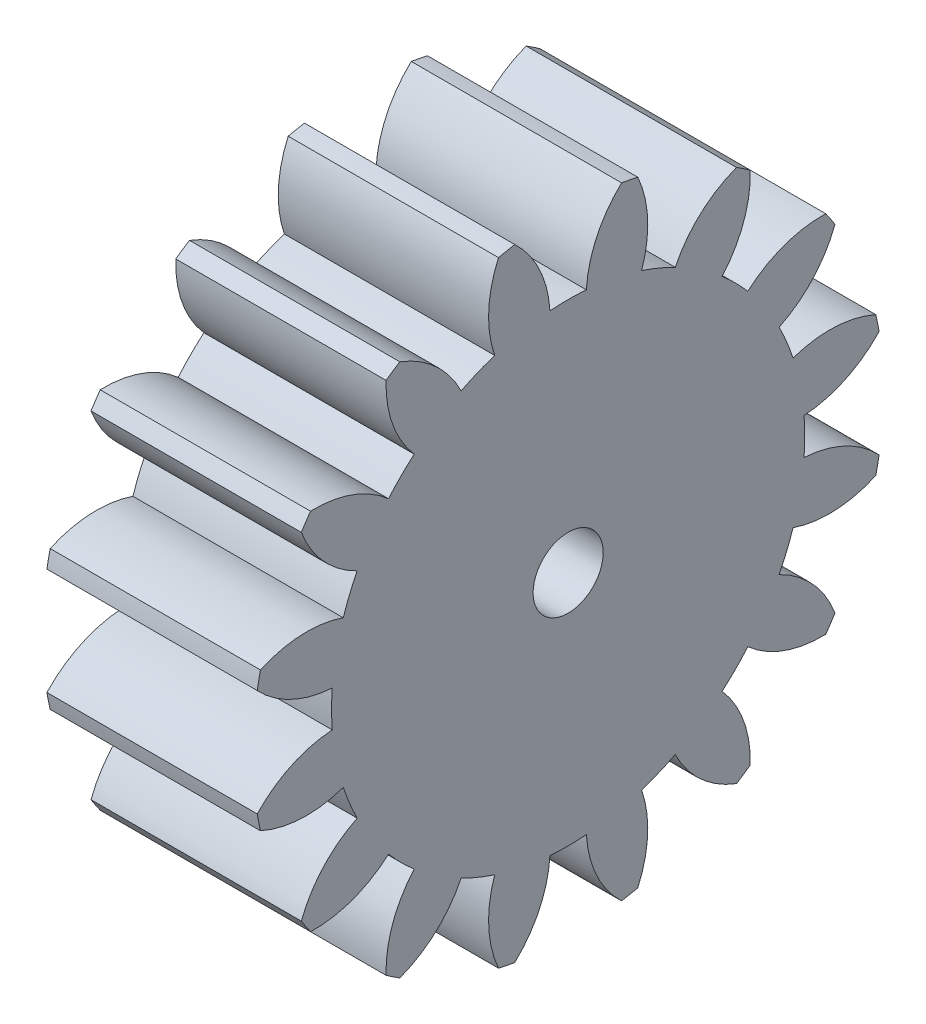
SolidWorks part; units mm, degrees
ref_plane "Plane1" through (0, 0, 0) normal (0, 0, 1) x (1, 0, 0)
ref_plane "Plane2" through (0, 0, 0) normal (0, 1, 0) x (1, 0, 0)
ref_plane "Plane3" through (0, 0, 0) normal (1, 0, 0) x (0, 0, -1)
sketch "HoldingSke" plane through (0, 0, 0) normal (0, 1, 0) x (1, 0, 0)
  line L0 (0, 0) -> (0.3845, -0.1103)
  line L1 (-15, 0) -> (100, 0) construction
  line L2 (0, 0) -> (-2.1039, 2.3779)
  line L3 (0, 0) -> (-11.863, 4.5341)
  line L4 (0, 0) -> (8.3015, 2.3804)
  line L5 (0, 0) -> (-46.8476, -17.4728)
  line L6 (0, 0) -> (-12.4344, -8.3896)
  line L7 (-2.1039, 2.3779) -> (8.6586, 51.2059)
  line L8 (-76.2, 54.61) -> (-75.3, 54.61)
  line L9 (-71.009, 38.7566) -> (-53.1078, 45.2721)
  line L10 (-76.2, 71.12) -> (104.1128, 71.12)
  line L11 (0, 0) -> (-15, 0)
  line L12 (-76.2, 101.6) -> (-76.113, 101.6)
  line L13 (24.9733, 27.94) -> (52.9518, 28.4284)
  line L14 (24.9733, 27.94) -> (24.9743, 27.94)
  line L15 (24.9733, 27.94) -> (100.4006, 29.5858)
  line L16 (-63.627, -2.5) -> (-12.827, -2.5)
  circle A0 centre (0, 0) radius 2.5
  circle A1 centre (0, 0) radius 16.874
  circle A2 centre (0, 0) radius 37.5
  circle A3 centre (0, 0) radius 2.5
  dimension "MHD" = 33.748
  dimension "Hub_dia" = 75
  dimension "Bore" = 5
  dimension "MBD" = 5
  dimension "Num_teeth" = 16
  dimension "Pitch" = 0.4
  dimension "Overall_len" = 50
  dimension "Show_teeth" = 16
  dimension "Thickness" = 15
  dimension "OAL" = 50.0001
  dimension "T_dim" = 0.9
  dimension "Ap" = 20
  dimension "H" = 19.05
  dimension "Pitch_radius" = 180.3128
  dimension "Width" = 15
  dimension "Backlash" = 0.087
  dimension "Addendum_fac" = 1
  dimension "Dedendum_fac" = 1.25
  dimension "Clearance_fac" = 0.25
  dimension "Dedendum_add" = 0.001
  dimension "Module" = 2.5
sketch "BasProSke" plane through (0, 0, 0) normal (0, 1, 0) x (1, 0, 0)
  line L0 (-10, 0) -> (60, 0) construction
  line L1 (0, 0) -> (0, 22.5)
  line L2 (0, 0) -> (15, 0)
  line L3 (15, 0) -> (15, 22.5)
  line L4 (15, 22.5) -> (0, 22.5)
  dimension "Thickness" = 15
  dimension "Diameter" = 45
revolve "Base-Revolve" add sketch "BasProSke" angle 360 about L0
sketch "TooCutSke" plane through (0, 0, 0) normal (1, 0, 0) x (0, 0, -1)
  line L1 (0, 0) -> (0, 107) construction
  line L2 (0, 0) -> (-2.1125, 19.8881) construction
  line L3 (0, 0) -> (-7.7717, 39.0708) construction
  line L4 (-2.1125, 19.8881) -> (-3.8858, 19.5354) construction
  arc A0 (1.2977, 16.824) -> (-1.2977, 16.824) centre (0, 0) ccw
  arc A1 (3.8326, 22.197) -> (-3.8326, 22.197) centre (0, 0) ccw
  circle A2 centre (0, 0) radius 20 construction
  circle A3 centre (0, 0) radius 18.7939 construction
  arc A4 (-1.2977, 16.824) -> (-3.8326, 22.197) centre (-9.2832, 16.3411) ccw
  arc A5 (3.8326, 22.197) -> (1.2977, 16.824) centre (9.2832, 16.3411) ccw
  dimension "Root_dia" = 33.748
  dimension "Overcut_dia" = 45.0508
  dimension "Pitch_dia" = 40
  dimension "Base_dia" = 37.5877
  dimension "Flank_rad" = 8
  dimension "Half_ang" = 11.25
  dimension "Half_CT" = 1.8081
extrude "ToothCut" cut sketch "TooCutSke" along normal through all
fillet "Breaks" [suppressed] radius 0.05
fillet "RootFillets" [suppressed] radius 0.626
pattern_circular "TeethCuts" count 16 every 22.5 about axis through (-10, 0, 0) along (1, 0, 0) of "ToothCut", "RootFillets", "Breaks"
sketch "HubNeaOneSke" plane through (0, 0, 0) normal (-1, 0, 0) x (0, 0, 1)
  circle A0 centre (0, 0) radius 16.874
  dimension "Diameter" = 33.748
extrude "HubNearOne" [suppressed] add sketch "HubNeaOneSke" along normal blind 35.0001
sketch "HubNeaBotSke" plane through (0, 0, 0) normal (-1, 0, 0) x (0, 0, 1)
  circle A0 centre (0, 0) radius 16.874
  dimension "Diameter" = 33.748
extrude "HubNearBoth" [suppressed] add sketch "HubNeaBotSke" along normal blind 17.5
ref_plane "FarPln" through (15, 0, 0) normal (1, 0, 0) x (0, 0, -1)
sketch "HubFarSke" plane through (15, 0, 0) normal (1, 0, 0) x (0, 0, -1)
  circle A0 centre (0, 0) radius 16.874
  dimension "Diameter" = 33.748
extrude "HubFar" [suppressed] add sketch "HubFarSke" along normal blind 17.5
sketch "BorSke" plane through (0, 0, 0) normal (1, 0, 0) x (0, 0, -1)
  circle A0 centre (0, 0) radius 2.5
  dimension "Diameter" = 5
extrude "Bore" cut sketch "BorSke" along normal mid plane 100.0001
sketch "KeySke" plane through (0, 0, 0) normal (1, 0, 0) x (0, 0, -1)
  line L0 (-1, 0) -> (-1, 3.4)
  line L1 (-1, 3.4) -> (1, 3.4)
  line L2 (1, 3.4) -> (1, 0)
  line L3 (0, 0) -> (0, 34) construction
  line L4 (-1, 0) -> (1, 0)
  dimension "Offset" = 3.4
  dimension "Width" = 2
extrude "Keyway" [suppressed] cut sketch "KeySke" along normal mid plane 100.0001
pattern_circular "Keyway2" [suppressed] count 2 every 90 about axis through (-10, 0, 0) along (1, 0, 0)
equation "' \"Module@HoldingSke\" = 6.35"
equation "' \"Num_teeth@HoldingSke\" = 12"
equation "' \"Ap@HoldingSke\" =  20"
equation "' \"Ap@HoldingSke\" = 20"
equation "' \"Width@HoldingSke\" = 0.5 * 25.4"
equation "' \"Hub_dia@HoldingSke\"= 1 * 25.4"
equation "' \"Hub_dia@HoldingSke\" = 1 * 25.4"
equation "' \"Overall_len@HoldingSke\" = 1.0 * 25.4"
equation "' \"Bore@HoldingSke\" = 0.75 * 25.4"
equation "' \"T_dim@HoldingSke\" = 0.1 * 25.4"
equation "' \"Width@KeySke\" = 0.25 * 25.4"
equation "' \"Show_teeth@HoldingSke\" = 13"
equation "' \"Backlash@HoldingSke\" = 0.009 * 25.4"
equation "' \"Addendum_fac@HoldingSke\" = 1.0"
equation "' \"Dedendum_fac@HoldingSke\" = 1.25"
equation "' \"Dedendum_add@HoldingSke\" = 0.00005 * 25.4"
equation "' \"Clearance_fac@HoldingSke\" = 0.25"
equation "\"Pitch@HoldingSke\" = 1 / \"Module@HoldingSke\""
equation "\"Overcut_dia@TooCutSke\" = (\"Num_teeth@HoldingSke\" + 2 * \"Addendum_fac@HoldingSke\") / \"Pitch@HoldingSke\" + 0.002 * 25.4"
equation "\"Pitch_dia@TooCutSke\" = \"Num_teeth@HoldingSke\" / \"Pitch@HoldingSke\""
equation "\"Base_dia@TooCutSke\" = \"Num_teeth@HoldingSke\" / \"Pitch@HoldingSke\" * cos((\"Ap@HoldingSke\"  * 3.14159265 / 180))"
equation "\"Root_dia@TooCutSke\" = (\"Num_teeth@HoldingSke\" + 2) / \"Pitch@HoldingSke\" - 2 * (\"Addendum_fac@HoldingSke\" + \"Dedendum_fac@HoldingSke\") / \"Pitch@HoldingSke\" - \"Dedendum_add@HoldingSke\" * 2"
equation "\"Half_ang@TooCutSke\" = 180 / \"Num_teeth@HoldingSke\""
equation "\"Half_CT@TooCutSke\" = \"Num_teeth@HoldingSke\" / \"Pitch@HoldingSke\" * sin((3.14159265 / 2 / \"Num_teeth@HoldingSke\")) / 2 - 7 * \"Backlash@HoldingSke\" / 4"
equation "\"Flank_rad@TooCutSke\" = \"Num_teeth@HoldingSke\" / \"Pitch@HoldingSke\" / 5"
equation "\"Radius@RootFillets\" = \"Clearance_fac@HoldingSke\" / \"Pitch@HoldingSke\" + \"Dedendum_add@HoldingSke\""
equation "\"Break_rad@Breaks\" = 0.02 / \"Pitch@HoldingSke\""
equation "\"Thickness@HoldingSke\" = \"Width@HoldingSke\""
equation "\"OAL@HoldingSke\" = \"Thickness@HoldingSke\""
equation "\"MHD@HoldingSke\" = (\"Num_teeth@HoldingSke\" + 2) / \"Pitch@HoldingSke\" - 2 * (\"Addendum_fac@HoldingSke\" + \"Dedendum_fac@HoldingSke\")  / \"Pitch@HoldingSke\" - \"Dedendum_add@HoldingSke\" * 2"
equation "\"MBD@HoldingSke\" = (\"Num_teeth@HoldingSke\" + 2) / \"Pitch@HoldingSke\" - 2 * (\"Addendum_fac@HoldingSke\" + \"Dedendum_fac@HoldingSke\")  / \"Pitch@HoldingSke\" - \"Dedendum_add@HoldingSke\" * 2 - 0.002 * 25.4"
equation "\"MHD@HoldingSke\" = ((sgn( \"MHD@HoldingSke\" - \"Hub_dia@HoldingSke\" )-1)*( \"MHD@HoldingSke\" - \"Hub_dia@HoldingSke\" ))/-2+ \"Hub_dia@HoldingSke\""
equation "\"MBD@HoldingSke\" = ((sgn( \"MBD@HoldingSke\" - \"Bore@HoldingSke\" )-1)*( \"MBD@HoldingSke\" - \"Bore@HoldingSke\" ))/-2+ \"Bore@HoldingSke\""
equation "\"OAL@HoldingSke\" = ((sgn( \"OAL@HoldingSke\" - \"Overall_len@HoldingSke\" )+1)*( \"OAL@HoldingSke\" - \"Overall_len@HoldingSke\" ))/2 + \"Overall_len@HoldingSke\" + 0.000002 * 25.4"
equation "\"Num_teeth@TeethCuts\" = int( \"Show_teeth@HoldingSke\" ) + 1"
equation "\"Num_teeth@TeethCuts\" = ((sgn( \"Num_teeth@TeethCuts\" - \"Num_teeth@HoldingSke\" )-1)*( \"Num_teeth@TeethCuts\" - \"Num_teeth@HoldingSke\" ))/-2+ \"Num_teeth@HoldingSke\""
equation "\"Num_teeth@TeethCuts\" = ((sgn( \"Num_teeth@TeethCuts\" - 2.0)+1)*( \"Num_teeth@TeethCuts\" - 2.0))/2 +2.0"
equation "\"Angle@TeethCuts\" = 360.0 / \"Num_teeth@HoldingSke\""
equation "\"Diameter@BasProSke\" = (\"Num_teeth@HoldingSke\" + 2 * \"Addendum_fac@HoldingSke\") / \"Pitch@HoldingSke\""
equation "\"Thickness@BasProSke\"  = \"Thickness@HoldingSke\""
equation "' \"Fillet_rad@BasProSke\" =  \"Thickness@HoldingSke\" * 0.05"
equation "' \"Fillet_rad@BasProSke\" = \"Thickness@HoldingSke\" * 0.05"
equation "\"MHD@HoldingSke\" = ((sgn( \"MHD@HoldingSke\" - \"Root_dia@TooCutSke\" )-1)*( \"MHD@HoldingSke\" - \"Root_dia@TooCutSke\" ))/-2+ \"Root_dia@TooCutSke\""
equation "\"Diameter@HubNeaOneSke\" = \"MHD@HoldingSke\""
equation "\"Length@HubNearOne\" = \"OAL@HoldingSke\" - \"Thickness@BasProSke\""
equation "\"Diameter@HubNeaBotSke\" = \"MHD@HoldingSke\""
equation "\"Length@HubNearBoth\" = ( \"OAL@HoldingSke\" - \"Thickness@BasProSke\" ) / 2.0"
equation "\"Thickness@FarPln\" = \"Thickness@BasProSke\""
equation "\"Diameter@HubFarSke\" = \"MHD@HoldingSke\""
equation "\"Length@HubFar\" = ( \"OAL@HoldingSke\" - \"Thickness@BasProSke\" ) / 2.0"
equation "\"Diameter@BorSke\" = \"MBD@HoldingSke\""
equation "\"D1@Bore\" = \"OAL@HoldingSke\" * 2.0"
equation "\"D1@Keyway\" = \"OAL@HoldingSke\" * 2.0"
equation "\"Offset@KeySke\" = \"T_dim@HoldingSke\" + \"MBD@HoldingSke\" / 2.0"
